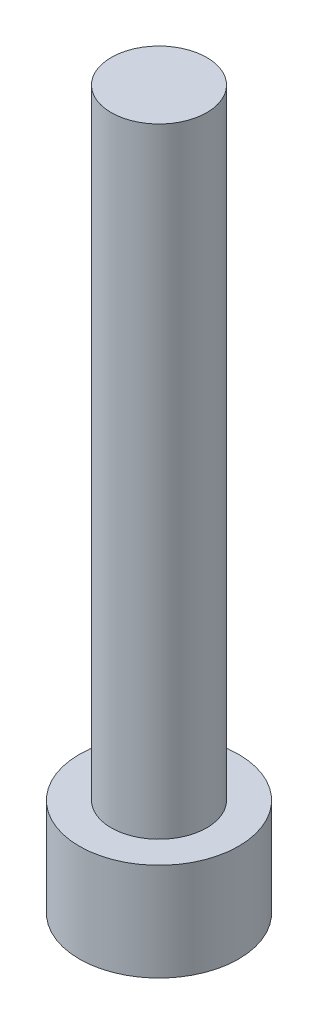
SolidWorks part; units mm, degrees
ref_plane "Front Plane" through (0, 0, 0) normal (0, 0, 1) x (1, 0, 0)
ref_plane "Top Plane" through (0, 0, 0) normal (0, 1, 0) x (1, 0, 0)
ref_plane "Right Plane" through (0, 0, 0) normal (1, 0, 0) x (0, 0, -1)
sketch "Sketch1" plane through (0, 0, 0) normal (0, 1, 0) x (1, 0, 0)
  circle A0 centre (0, 0) radius 2.8575
  dimension "D1" = 5.715
extrude "Boss-Extrude1" add sketch "Sketch1" along normal blind 3.5052
sketch "Sketch2" plane through (0, 0, 0) normal (0, -1, 0) x (1, 0, 0)
  line L1 (1.604, 0) -> (0.802, 1.3891)
  line L2 (0.802, 1.3891) -> (-0.802, 1.3891)
  line L3 (-0.802, 1.3891) -> (-1.604, 0)
  line L4 (-1.604, 0) -> (-0.802, -1.3891)
  line L5 (-0.802, -1.3891) -> (0.802, -1.3891)
  line L6 (0.802, -1.3891) -> (1.604, 0)
  circle A0 centre (0, 0) radius 1.3891 construction
  dimension "D1" = 2.7781
extrude "Cut-Extrude1" cut sketch "Sketch2" against normal blind 1.9558
sketch "Sketch3" plane through (0, 3.5052, 0) normal (0, 1, 0) x (1, 0, 0)
  circle A0 centre (0, 0) radius 1.7145
  dimension "D1" = 3.429
extrude "Boss-Extrude2" add sketch "Sketch3" along normal blind 22.225
